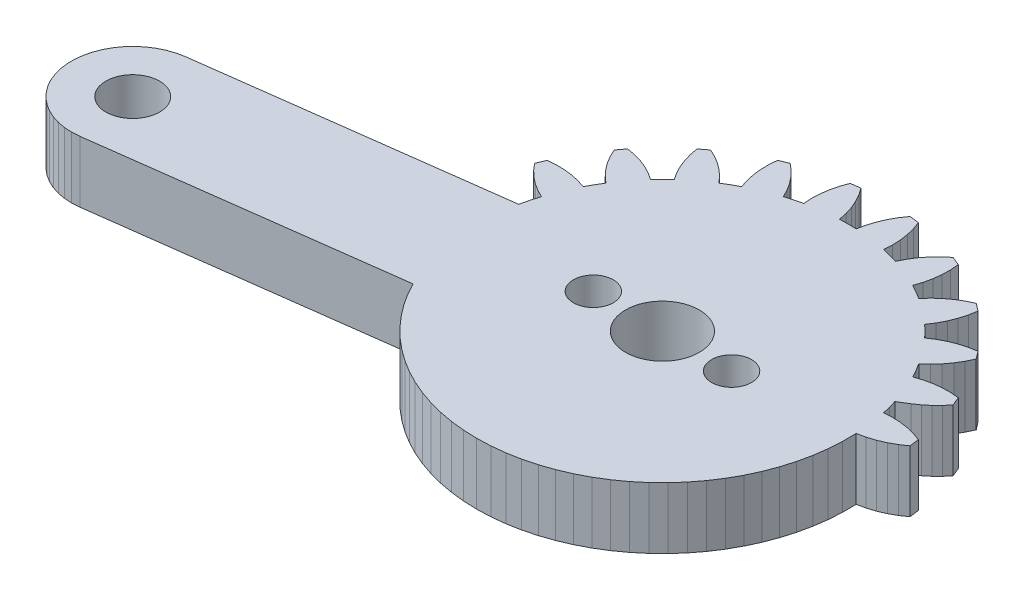
SolidWorks part; units mm, degrees
ref_plane "Front Plane" through (0, 0, 0) normal (0, 0, 1) x (1, 0, 0)
ref_plane "Top Plane" through (0, 0, 0) normal (0, 1, 0) x (1, 0, 0)
ref_plane "Right Plane" through (0, 0, 0) normal (1, 0, 0) x (0, 0, -1)
ref_plane "Plane1" through (0, 0, 0) normal (0, -1, 0) x (1, 0, 0)
sketch "Sketch1" plane through (0, 0, 0) normal (0, -1, 0) x (1, 0, 0)
  line L36 (36.2492, 26.501) -> (35.3663, 26.598)
  line L37 (35.3663, 26.598) -> (34.4786, 26.6301)
  line L38 (34.4786, 26.6301) -> (33.5909, 26.5968)
  line L39 (33.5909, 26.5968) -> (32.7081, 26.4985)
  line L40 (32.7081, 26.4985) -> (31.8349, 26.3357)
  line L41 (31.8349, 26.3357) -> (30.976, 26.1092)
  line L42 (30.976, 26.1092) -> (30.136, 25.8202)
  line L43 (30.136, 25.8202) -> (29.3195, 25.4704)
  line L44 (29.3195, 25.4704) -> (28.5309, 25.0616)
  line L45 (28.5309, 25.0616) -> (27.7744, 24.596)
  line L46 (27.7744, 24.596) -> (27.0541, 24.0761)
  line L47 (27.0541, 24.0761) -> (26.374, 23.5048)
  line L48 (26.374, 23.5048) -> (25.7376, 22.885)
  line L49 (25.7376, 22.885) -> (25.1485, 22.2203)
  line L50 (25.1485, 22.2203) -> (24.6097, 21.514)
  line L51 (24.6097, 21.514) -> (24.1242, 20.7702)
  line L52 (24.1242, 20.7702) -> (23.6946, 19.9927)
  line L53 (23.6946, 19.9927) -> (4.5221, 22.5168)
  line L54 (4.5221, 22.5168) -> (4.0209, 22.5509)
  line L55 (4.0209, 22.5509) -> (3.5195, 22.522)
  line L56 (3.5195, 22.522) -> (3.0255, 22.4305)
  line L57 (3.0255, 22.4305) -> (2.547, 22.2778)
  line L58 (2.547, 22.2778) -> (2.0914, 22.0663)
  line L59 (2.0914, 22.0663) -> (1.6658, 21.7993)
  line L60 (1.6658, 21.7993) -> (1.2771, 21.4812)
  line L61 (1.2771, 21.4812) -> (0.9313, 21.1168)
  line L62 (0.9313, 21.1168) -> (0.634, 20.712)
  line L63 (0.634, 20.712) -> (0.3897, 20.273)
  line L64 (0.3897, 20.273) -> (0.2023, 19.807)
  line L65 (0.2023, 19.807) -> (0.0748, 19.3211)
  line L66 (0.0748, 19.3211) -> (0.0093, 18.8231)
  line L67 (0.0093, 18.8231) -> (0.0066, 18.3207)
  line L68 (0.0066, 18.3207) -> (0.067, 17.822)
  line L69 (0.067, 17.822) -> (0.1894, 17.3349)
  line L70 (0.1894, 17.3349) -> (0.3718, 16.8668)
  line L71 (0.3718, 16.8668) -> (0.6115, 16.4254)
  line L72 (0.6115, 16.4254) -> (0.9046, 16.0175)
  line L73 (0.9046, 16.0175) -> (1.2466, 15.6495)
  line L74 (1.2466, 15.6495) -> (1.6319, 15.3273)
  line L75 (1.6319, 15.3273) -> (2.0547, 15.0559)
  line L76 (2.0547, 15.0559) -> (2.508, 14.8397)
  line L77 (2.508, 14.8397) -> (2.985, 14.6819)
  line L78 (2.985, 14.6819) -> (3.4779, 14.5852)
  line L79 (3.4779, 14.5852) -> (22.6504, 12.0611)
  line L80 (22.6504, 12.0611) -> (22.7897, 11.4699)
  line L81 (22.7897, 11.4699) -> (22.9585, 10.8864)
  line L82 (22.9585, 10.8864) -> (22.4762, 10.6428)
  line L83 (22.4762, 10.6428) -> (22.0208, 10.3523)
  line L84 (22.0208, 10.3523) -> (21.5966, 10.0177)
  line L85 (21.5966, 10.0177) -> (21.208, 9.6424)
  line L86 (21.208, 9.6424) -> (20.8588, 9.2302)
  line L87 (20.8588, 9.2302) -> (21.0977, 8.6535)
  line L88 (21.0977, 8.6535) -> (21.6361, 8.6089)
  line L89 (21.6361, 8.6089) -> (22.1763, 8.6183)
  line L90 (22.1763, 8.6183) -> (22.7128, 8.6817)
  line L91 (22.7128, 8.6817) -> (23.2403, 8.7983)
  line L92 (23.2403, 8.7983) -> (23.7535, 8.967)
  line L93 (23.7535, 8.967) -> (24.0143, 8.4909)
  line L94 (24.0143, 8.4909) -> (24.2962, 8.027)
  line L95 (24.2962, 8.027) -> (23.8935, 7.6669)
  line L96 (23.8935, 7.6669) -> (23.5287, 7.2684)
  line L97 (23.5287, 7.2684) -> (23.2056, 6.8355)
  line L98 (23.2056, 6.8355) -> (22.9274, 6.3724)
  line L99 (22.9274, 6.3724) -> (22.6968, 5.8838)
  line L100 (22.6968, 5.8838) -> (23.0768, 5.3886)
  line L101 (23.0768, 5.3886) -> (23.6084, 5.4849)
  line L102 (23.6084, 5.4849) -> (24.1277, 5.6338)
  line L103 (24.1277, 5.6338) -> (24.6295, 5.8338)
  line L104 (24.6295, 5.8338) -> (25.1089, 6.083)
  line L105 (25.1089, 6.083) -> (25.5609, 6.3788)
  line L106 (25.5609, 6.3788) -> (25.9361, 5.9864)
  line L107 (25.9361, 5.9864) -> (26.3284, 5.6113)
  line L108 (26.3284, 5.6113) -> (26.0326, 5.1593)
  line L109 (26.0326, 5.1593) -> (25.7834, 4.6799)
  line L110 (25.7834, 4.6799) -> (25.5834, 4.1781)
  line L111 (25.5834, 4.1781) -> (25.4345, 3.6587)
  line L112 (25.4345, 3.6587) -> (25.3382, 3.1272)
  line L113 (25.3382, 3.1272) -> (25.8334, 2.7472)
  line L114 (25.8334, 2.7472) -> (26.322, 2.9777)
  line L115 (26.322, 2.9777) -> (26.7851, 3.256)
  line L116 (26.7851, 3.256) -> (27.218, 3.5791)
  line L117 (27.218, 3.5791) -> (27.6166, 3.9438)
  line L118 (27.6166, 3.9438) -> (27.9766, 4.3466)
  line L119 (27.9766, 4.3466) -> (28.4405, 4.0647)
  line L120 (28.4405, 4.0647) -> (28.9167, 3.8039)
  line L121 (28.9167, 3.8039) -> (28.7479, 3.2907)
  line L122 (28.7479, 3.2907) -> (28.6313, 2.7632)
  line L123 (28.6313, 2.7632) -> (28.5679, 2.2266)
  line L124 (28.5679, 2.2266) -> (28.5585, 1.6865)
  line L125 (28.5585, 1.6865) -> (28.6031, 1.1481)
  line L126 (28.6031, 1.1481) -> (29.1798, 0.9092)
  line L127 (29.1798, 0.9092) -> (29.592, 1.2584)
  line L128 (29.592, 1.2584) -> (29.9673, 1.647)
  line L129 (29.9673, 1.647) -> (30.3019, 2.0712)
  line L130 (30.3019, 2.0712) -> (30.5925, 2.5266)
  line L131 (30.5925, 2.5266) -> (30.836, 3.0089)
  line L132 (30.836, 3.0089) -> (31.3571, 2.8566)
  line L133 (31.3571, 2.8566) -> (31.8845, 2.7279)
  line L134 (31.8845, 2.7279) -> (31.8543, 2.1885)
  line L135 (31.8543, 2.1885) -> (31.8782, 1.6488)
  line L136 (31.8782, 1.6488) -> (31.9558, 1.1142)
  line L137 (31.9558, 1.1142) -> (32.0866, 0.59)
  line L138 (32.0866, 0.59) -> (32.269, 0.0815)
  line L139 (32.269, 0.0815) -> (32.8878, 0)
  line L140 (32.8878, 0) -> (33.1957, 0.444)
  line L141 (33.1957, 0.444) -> (33.4576, 0.9165)
  line L142 (33.4576, 0.9165) -> (33.671, 1.4128)
  line L143 (33.671, 1.4128) -> (33.8337, 1.9279)
  line L144 (33.8337, 1.9279) -> (33.9442, 2.4568)
  line L145 (33.9442, 2.4568) -> (34.4869, 2.4446)
  line L146 (34.4869, 2.4446) -> (35.0296, 2.4568)
  line L147 (35.0296, 2.4568) -> (35.1401, 1.9279)
  line L148 (35.1401, 1.9279) -> (35.3029, 1.4128)
  line L149 (35.3029, 1.4128) -> (35.5163, 0.9165)
  line L150 (35.5163, 0.9165) -> (35.7782, 0.444)
  line L151 (35.7782, 0.444) -> (36.086, 0)
  line L152 (36.086, 0) -> (36.7049, 0.0815)
  line L153 (36.7049, 0.0815) -> (36.8873, 0.59)
  line L154 (36.8873, 0.59) -> (37.018, 1.1142)
  line L155 (37.018, 1.1142) -> (37.0957, 1.6488)
  line L156 (37.0957, 1.6488) -> (37.1196, 2.1885)
  line L157 (37.1196, 2.1885) -> (37.0894, 2.7279)
  line L158 (37.0894, 2.7279) -> (37.6168, 2.8566)
  line L159 (37.6168, 2.8566) -> (38.1378, 3.0089)
  line L160 (38.1378, 3.0089) -> (38.3814, 2.5266)
  line L161 (38.3814, 2.5266) -> (38.6719, 2.0712)
  line L162 (38.6719, 2.0712) -> (39.0065, 1.647)
  line L163 (39.0065, 1.647) -> (39.3818, 1.2584)
  line L164 (39.3818, 1.2584) -> (39.7941, 0.9092)
  line L165 (39.7941, 0.9092) -> (40.3707, 1.1481)
  line L166 (40.3707, 1.1481) -> (40.4153, 1.6865)
  line L167 (40.4153, 1.6865) -> (40.4059, 2.2266)
  line L168 (40.4059, 2.2266) -> (40.3426, 2.7632)
  line L169 (40.3426, 2.7632) -> (40.2259, 3.2907)
  line L170 (40.2259, 3.2907) -> (40.0572, 3.8039)
  line L171 (40.0572, 3.8039) -> (40.5333, 4.0647)
  line L172 (40.5333, 4.0647) -> (40.9972, 4.3466)
  line L173 (40.9972, 4.3466) -> (41.3573, 3.9438)
  line L174 (41.3573, 3.9438) -> (41.7558, 3.5791)
  line L175 (41.7558, 3.5791) -> (42.1888, 3.256)
  line L176 (42.1888, 3.256) -> (42.6519, 2.9777)
  line L177 (42.6519, 2.9777) -> (43.1404, 2.7472)
  line L178 (43.1404, 2.7472) -> (43.6356, 3.1272)
  line L179 (43.6356, 3.1272) -> (43.5394, 3.6587)
  line L180 (43.5394, 3.6587) -> (43.3905, 4.1781)
  line L181 (43.3905, 4.1781) -> (43.1904, 4.6799)
  line L182 (43.1904, 4.6799) -> (42.9412, 5.1593)
  line L183 (42.9412, 5.1593) -> (42.6454, 5.6113)
  line L184 (42.6454, 5.6113) -> (43.0378, 5.9864)
  line L185 (43.0378, 5.9864) -> (43.4129, 6.3788)
  line L186 (43.4129, 6.3788) -> (43.865, 6.083)
  line L187 (43.865, 6.083) -> (44.3443, 5.8338)
  line L188 (44.3443, 5.8338) -> (44.8462, 5.6338)
  line L189 (44.8462, 5.6338) -> (45.3655, 5.4849)
  line L190 (45.3655, 5.4849) -> (45.8971, 5.3886)
  line L191 (45.8971, 5.3886) -> (46.2771, 5.8838)
  line L192 (46.2771, 5.8838) -> (46.0465, 6.3724)
  line L193 (46.0465, 6.3724) -> (45.7683, 6.8355)
  line L194 (45.7683, 6.8355) -> (45.4452, 7.2684)
  line L195 (45.4452, 7.2684) -> (45.0804, 7.6669)
  line L196 (45.0804, 7.6669) -> (44.6776, 8.027)
  line L197 (44.6776, 8.027) -> (44.9596, 8.4909)
  line L198 (44.9596, 8.4909) -> (45.2204, 8.967)
  line L199 (45.2204, 8.967) -> (45.7336, 8.7983)
  line L200 (45.7336, 8.7983) -> (46.2611, 8.6817)
  line L201 (46.2611, 8.6817) -> (46.7976, 8.6183)
  line L202 (46.7976, 8.6183) -> (47.3378, 8.6089)
  line L203 (47.3378, 8.6089) -> (47.8762, 8.6535)
  line L204 (47.8762, 8.6535) -> (48.115, 9.2302)
  line L205 (48.115, 9.2302) -> (47.8009, 9.6046)
  line L206 (47.8009, 9.6046) -> (47.4543, 9.9491)
  line L207 (47.4543, 9.9491) -> (47.0779, 10.2609)
  line L208 (47.0779, 10.2609) -> (46.6749, 10.5373)
  line L209 (46.6749, 10.5373) -> (46.0313, 10.9372)
  line L210 (46.0313, 10.9372) -> (46.1745, 11.4332)
  line L211 (46.1745, 11.4332) -> (46.2963, 11.9349)
  line L212 (46.2963, 11.9349) -> (46.8357, 11.9047)
  line L213 (46.8357, 11.9047) -> (47.3754, 11.9286)
  line L214 (47.3754, 11.9286) -> (47.9101, 12.0062)
  line L215 (47.9101, 12.0062) -> (48.4343, 12.137)
  line L216 (48.4343, 12.137) -> (48.9428, 12.3194)
  line L217 (48.9428, 12.3194) -> (49.0242, 12.9382)
  line L218 (49.0242, 12.9382) -> (48.5803, 13.2461)
  line L219 (48.5803, 13.2461) -> (48.1078, 13.508)
  line L220 (48.1078, 13.508) -> (47.6115, 13.7214)
  line L221 (47.6115, 13.7214) -> (47.0963, 13.8841)
  line L222 (47.0963, 13.8841) -> (46.5675, 13.9946)
  line L223 (46.5675, 13.9946) -> (46.5747, 14.8828)
  line L224 (46.5747, 14.8828) -> (46.5168, 15.7692)
  line L225 (46.5168, 15.7692) -> (46.3939, 16.649)
  line L226 (46.3939, 16.649) -> (46.2067, 17.5173)
  line L227 (46.2067, 17.5173) -> (45.9564, 18.3696)
  line L228 (45.9564, 18.3696) -> (45.6441, 19.2012)
  line L229 (45.6441, 19.2012) -> (45.2717, 20.0076)
  line L230 (45.2717, 20.0076) -> (44.841, 20.7845)
  line L231 (44.841, 20.7845) -> (44.3545, 21.5277)
  line L232 (44.3545, 21.5277) -> (43.8148, 22.2332)
  line L233 (43.8148, 22.2332) -> (43.2247, 22.8971)
  line L234 (43.2247, 22.8971) -> (42.5875, 23.516)
  line L235 (42.5875, 23.516) -> (41.9065, 24.0864)
  line L236 (41.9065, 24.0864) -> (41.1855, 24.6052)
  line L237 (41.1855, 24.6052) -> (40.4284, 25.0698)
  line L238 (40.4284, 25.0698) -> (39.6392, 25.4775)
  line L239 (39.6392, 25.4775) -> (38.8223, 25.8262)
  line L240 (38.8223, 25.8262) -> (37.9819, 26.114)
  line L241 (37.9819, 26.114) -> (37.1227, 26.3393)
  line L242 (37.1227, 26.3393) -> (36.2492, 26.501)
  circle A0 centre (4.0017, 18.5574) radius 1.75
  circle A2 centre (38.9914, 14.5352) radius 1.3
  circle A3 centre (34.4869, 14.5373) radius 2.4
  circle A4 centre (29.9869, 14.5373) radius 1.3
extrude "Boss-Extrude1" add sketch "Sketch1" against normal blind 4
